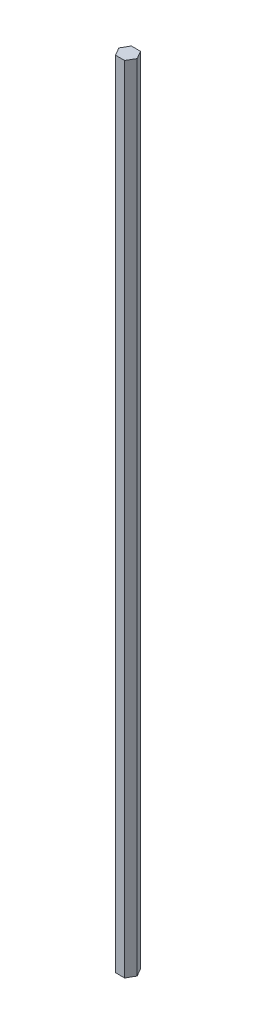
SolidWorks part; units mm, degrees
ref_plane "Front Plane" through (0, 0, 0) normal (0, 0, 1) x (1, 0, 0)
ref_plane "Top Plane" through (0, 0, 0) normal (0, 1, 0) x (1, 0, 0)
ref_plane "Right Plane" through (0, 0, 0) normal (1, 0, 0) x (0, 0, -1)
sketch "Sketch1" plane through (0, 0, 0) normal (0, 1, 0) x (1, 0, 0)
  line L1 (3.6662, -6.35) -> (7.3323, 0)
  line L2 (7.3323, 0) -> (3.6662, 6.35)
  line L3 (3.6662, 6.35) -> (-3.6662, 6.35)
  line L4 (-3.6662, 6.35) -> (-7.3323, 0)
  line L5 (-7.3323, 0) -> (-3.6662, -6.35)
  line L6 (-3.6662, -6.35) -> (3.6662, -6.35)
  circle A0 centre (0, 0) radius 6.35 construction
  dimension "D1" = 12.7
extrude "Boss-Extrude1" add sketch "Sketch1" along normal blind 635
